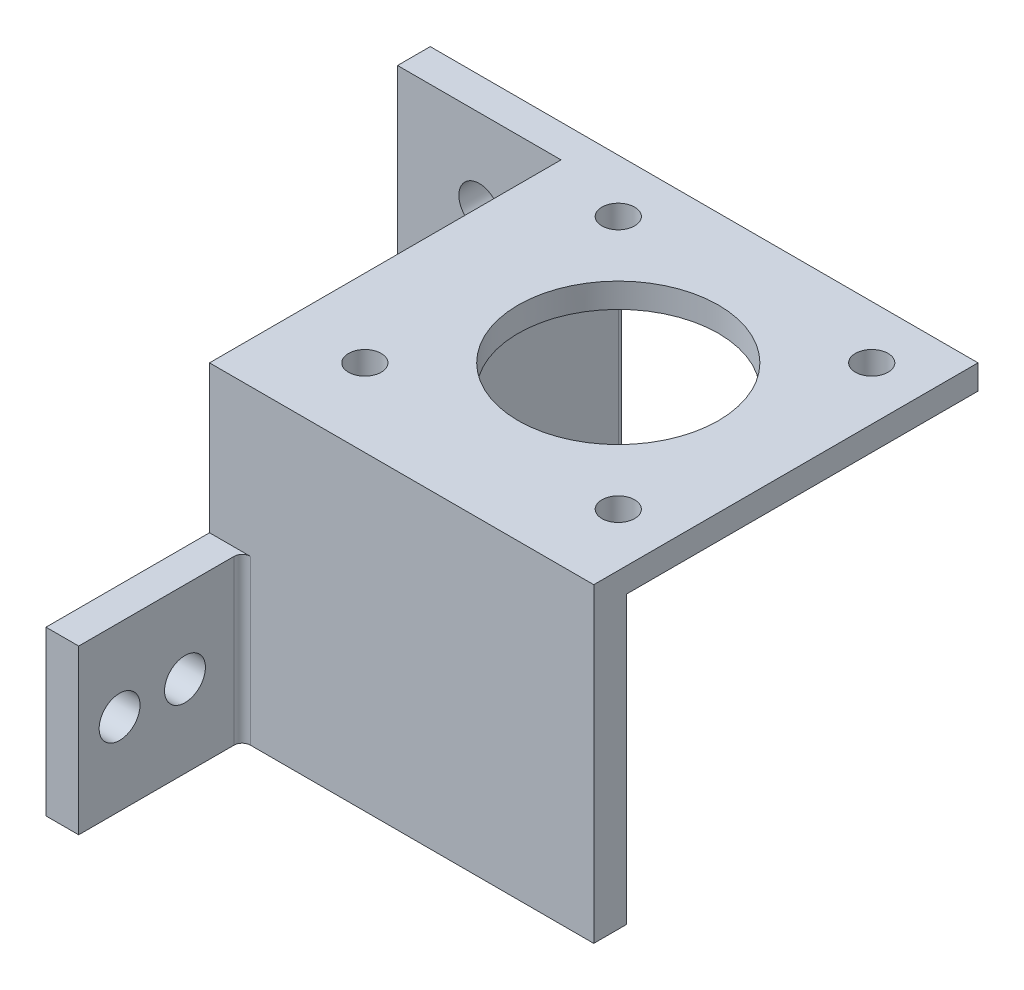
SolidWorks part; units mm, degrees
ref_plane "Front Plane" through (0, 0, 0) normal (0, 0, 1) x (1, 0, 0)
ref_plane "Top Plane" through (0, 0, 0) normal (0, 1, 0) x (1, 0, 0)
ref_plane "Right Plane" through (0, 0, 0) normal (1, 0, 0) x (0, 0, -1)
sketch "Sketch1" plane through (0, 0, 0) normal (0, 1, 0) x (1, 0, 0)
  line L0 (0, 0) -> (0, 34)
  line L1 (0, 34) -> (-20, 34)
  line L2 (-20, 34) -> (-20, 38)
  line L3 (-20, 38) -> (4, 38)
  line L4 (4, 38) -> (4, -5)
  line L5 (4, -5) -> (47, -5)
  line L6 (47, -5) -> (47, -9)
  line L7 (47, -9) -> (0, -9)
  line L8 (0, -9) -> (0, 0)
  dimension "D1" = 4
  dimension "D2" = 4
  dimension "D3" = 43
  dimension "D4" = 24
  dimension "D5" = 20
  dimension "D6" = 43
extrude "Boss-Extrude1" add sketch "Sketch1" along normal blind 38
sketch "Sketch2" plane through (0, 38, 0) normal (0, 1, 0) x (1, 0, 0)
  line L1 (4, -5) -> (47, -5)
  line L2 (4, -5) -> (4, 38)
  line L3 (4, 38) -> (47, 38)
  line L4 (47, -5) -> (47, 38)
  dimension "D1" = 43
  dimension "D2" = 43
extrude "Boss-Extrude2" add sketch "Sketch2" against normal blind 3
sketch "Sketch3" plane through (0, 35, 0) normal (0, -1, 0) x (-1, 0, 0)
  circle A0 centre (-40.5, 31.5) radius 2
  circle A1 centre (-9.5, 31.5) radius 2
  circle A2 centre (-9.5, 0.5) radius 2
  circle A3 centre (-40.5, 0.5) radius 2
  circle A4 centre (-25, 16) radius 12.25
  dimension "D1" = 4
  dimension "D2" = 4
  dimension "D3" = 4
  dimension "D4" = 4
extrude "Cut-Extrude1" cut sketch "Sketch3" against normal blind 10
sketch "Sketch4" plane through (0, 0, -34) normal (0, 0, 1) x (1, 0, 0)
  line L0 (-10, 0) -> (-10, 38) construction
  line L1 (-20, 0) -> (0, 0) construction
  line L2 (-20, 38) -> (0, 38) construction
  circle A0 centre (-10, 10) radius 2.5
  circle A1 centre (-10, 28) radius 2.5
  dimension "D1" = 5
  dimension "D2" = 5
  dimension "D3" = 10
  dimension "D4" = 10
extrude "Cut-Extrude2" cut sketch "Sketch4" against normal blind 10
sketch "Sketch5" plane through (0, 0, 0) normal (-1, 0, 0) x (0, 0, 1)
  line L0 (9, 10) -> (29, 10) construction
  line L1 (9, 0) -> (29, 0)
  line L2 (9, 0) -> (9, 20)
  line L3 (9, 20) -> (29, 20)
  line L4 (29, 0) -> (29, 20)
  circle A0 centre (16, 10) radius 2.5
  circle A1 centre (24, 10) radius 2.5
  dimension "D3" = 5
  dimension "D4" = 5
  dimension "D1" = 20
  dimension "D2" = 20
  dimension "D5" = 7
  dimension "D6" = 5
extrude "Boss-Extrude3" add sketch "Sketch5" against normal blind 4
fillet "Fillet1" radius 1 2 edges at (4, 17.5, -38) (4, 10, 9)
